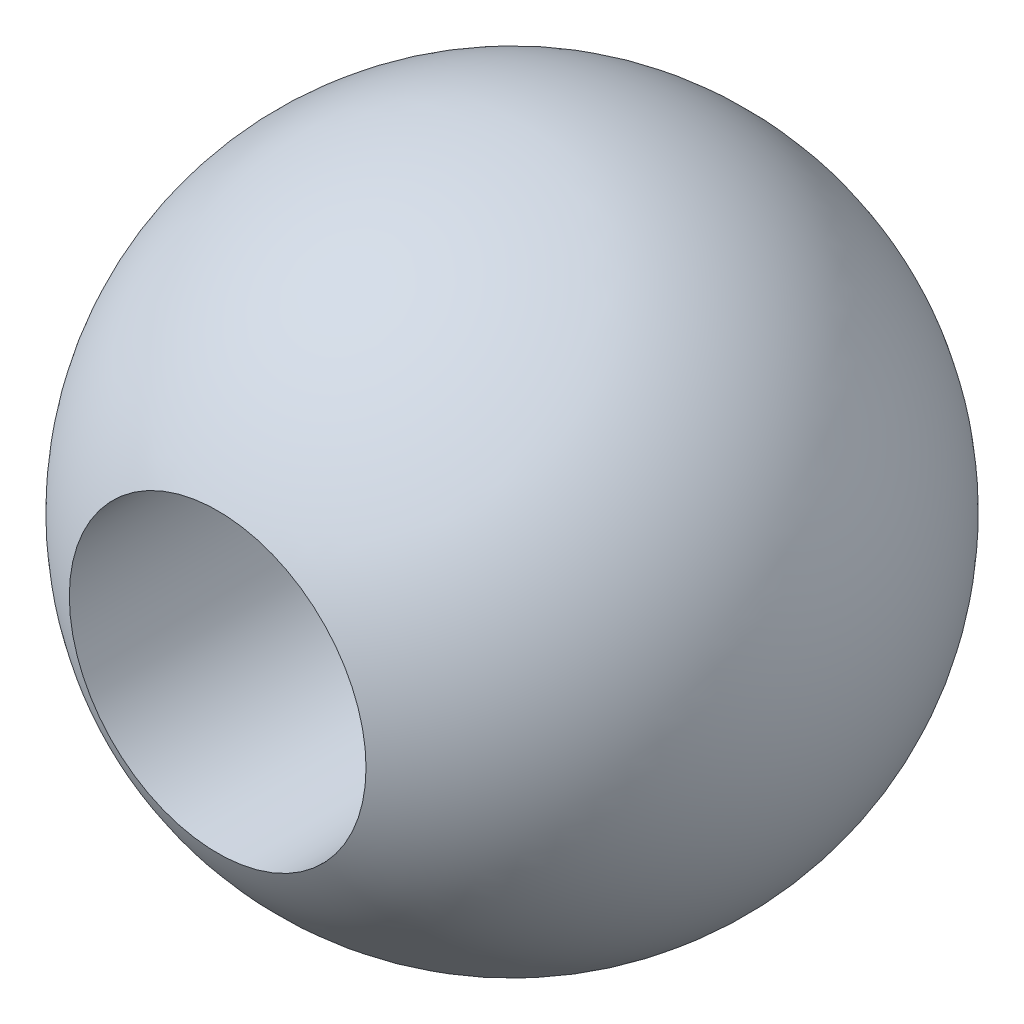
SolidWorks part; units mm, degrees
ref_plane "Front Plane" through (0, 0, 0) normal (0, 0, 1) x (1, 0, 0)
ref_plane "Top Plane" through (0, 0, 0) normal (0, 1, 0) x (1, 0, 0)
ref_plane "Right Plane" through (0, 0, 0) normal (1, 0, 0) x (0, 0, -1)
sketch "Sketch2" plane through (0, 0, 0) normal (0, 0, 1) x (1, 0, 0)
  line L0 (0, 0) -> (0, 50000) construction
  line L1 (0, 5.555) -> (0, -5.555)
  arc A1 (0, 5.555) -> (0, -5.555) centre (0, 0) ccw
  dimension "D2" = 11.11
revolve "Revolve3" add sketch "Sketch2" angle 360 about L0
sketch "Sketch3" plane through (0, 0, 0) normal (0, 0, 1) x (1, 0, 0)
  circle A0 centre (0, 0) radius 2.5
  dimension "D1" = 5
extrude "Cut-Extrude1" cut sketch "Sketch3" against normal through all both and the other way through all
